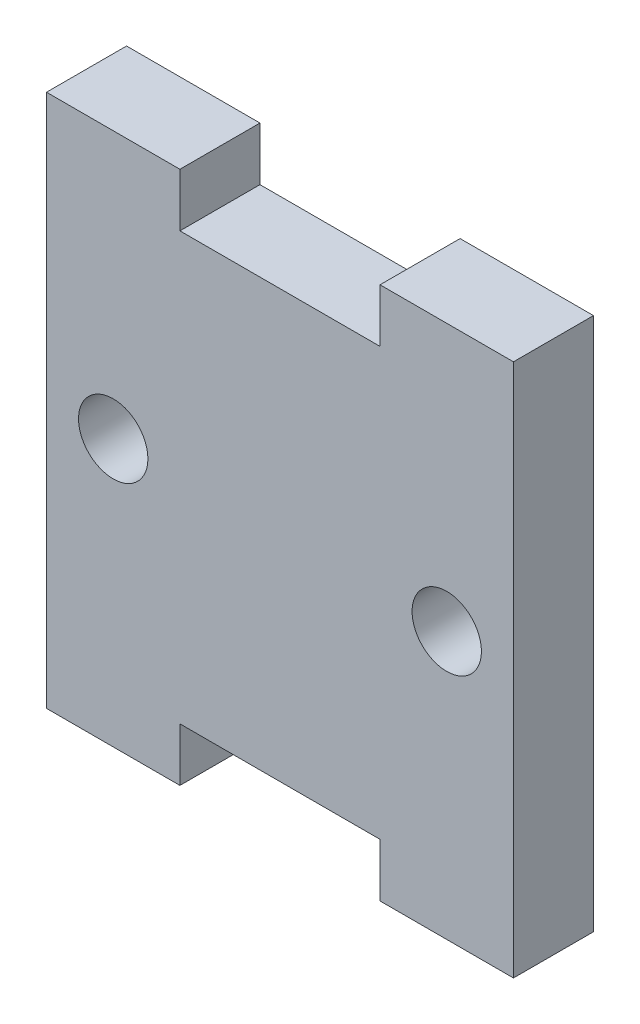
SolidWorks part; units mm, degrees
material "MDF"
ref_plane "Plano frontal" through (0, 0, 0) normal (0, 0, 1) x (1, 0, 0)
ref_plane "Plano superior" through (0, 0, 0) normal (0, 1, 0) x (1, 0, 0)
ref_plane "Plano direito" through (0, 0, 0) normal (1, 0, 0) x (0, 0, -1)
sketch "Esboço1" plane through (0, 0, 0) normal (0, 0, 1) x (1, 0, 0)
  line L0 (0, 0) -> (0, 16) construction
  line L1 (-17.5, -16) -> (17.5, -16)
  line L2 (-17.5, -16) -> (-17.5, 16)
  line L3 (-17.5, 16) -> (17.5, 16)
  line L4 (17.5, -16) -> (17.5, 16)
  line L5 (-17.5, -16) -> (17.5, 16) construction
  line L6 (-17.5, 16) -> (17.5, -16) construction
  line L7 (0, 0) -> (12.5, 0) construction
  line L8 (-7.5, -20) -> (-17.5, -20)
  line L9 (-7.5, -20) -> (-7.5, -16)
  line L10 (-7.5, -16) -> (-17.5, -16)
  line L11 (-17.5, -20) -> (-17.5, -16)
  line L12 (-7.5, -20) -> (-17.5, -16) construction
  line L13 (-7.5, -16) -> (-17.5, -20) construction
  line L14 (7.5, -20) -> (17.5, -20)
  line L15 (7.5, -20) -> (7.5, -16)
  line L16 (7.5, -16) -> (17.5, -16)
  line L17 (17.5, -20) -> (17.5, -16)
  line L18 (7.5, -20) -> (17.5, -16) construction
  line L19 (7.5, -16) -> (17.5, -20) construction
  line L20 (-7.5, 16) -> (-17.5, 16)
  line L21 (-17.5, 20) -> (-17.5, 16)
  line L22 (-7.5, 20) -> (-17.5, 20)
  line L23 (-7.5, 20) -> (-7.5, 16)
  line L24 (7.5, 16) -> (17.5, 16)
  line L25 (17.5, 20) -> (17.5, 16)
  line L26 (7.5, 20) -> (17.5, 20)
  line L27 (7.5, 20) -> (7.5, 16)
  circle A0 centre (-12.5, 0) radius 2.6
  circle A1 centre (12.5, 0) radius 2.6
  point P0 (0, 0)
  point P12 (-12.5, -18)
  point P13 (12.5, -18)
  dimension "D4" = 5.2
  dimension "D1" = 35
  dimension "D2" = 32
  dimension "D5" = 15
  dimension "D6" = 4
extrude "Ressalto-extrusão1" add sketch "Esboço1" along normal blind 6 contours L11 L8 L9 L1 | L1 L4 L3 L2 A0 A1 | L14 L17 L1 L15 | L26 L27 L3 L25 | L23 L22 L21 L3
